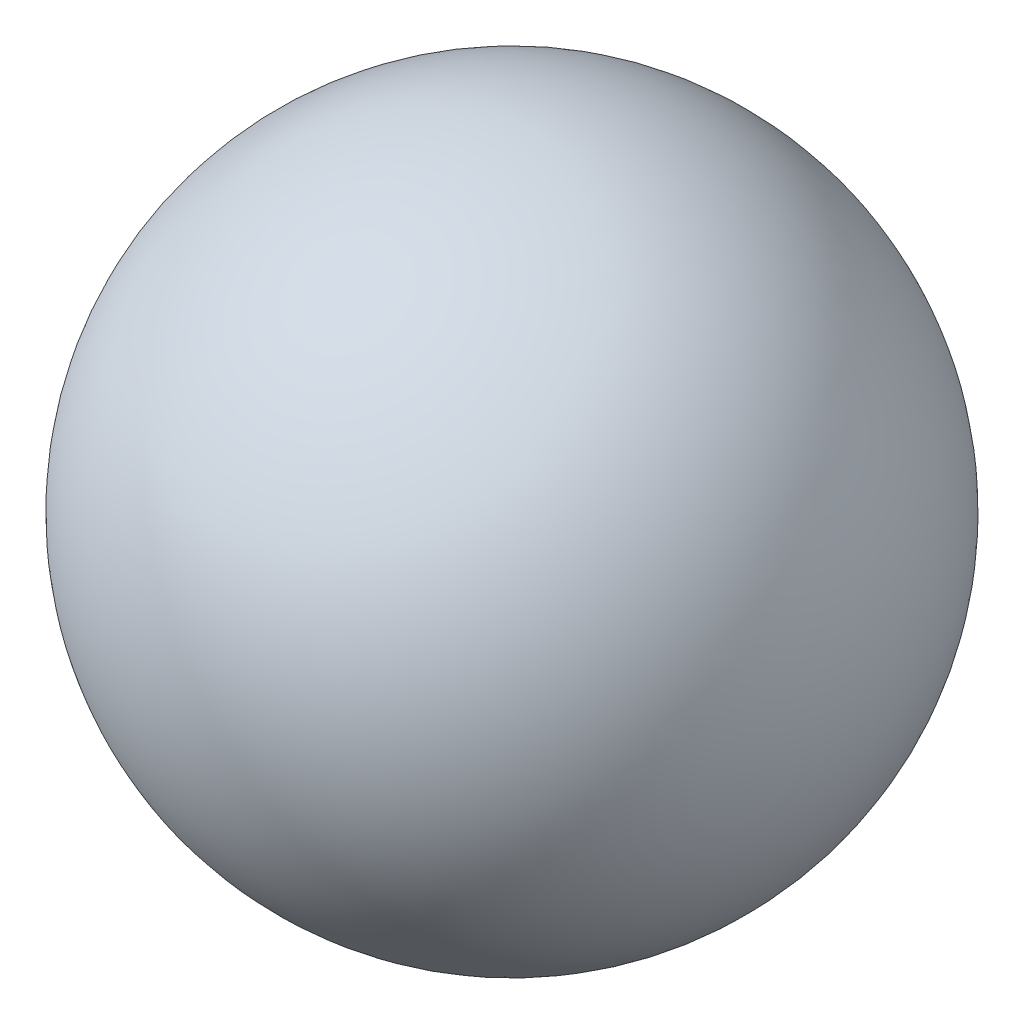
SolidWorks part; units mm, degrees
ref_plane "前基準面" through (0, 0, 0) normal (0, 0, 1) x (1, 0, 0)
ref_plane "上基準面" through (0, 0, 0) normal (0, 1, 0) x (1, 0, 0)
ref_plane "右基準面" through (0, 0, 0) normal (1, 0, 0) x (0, 0, -1)
sketch "草圖1" plane through (0, 0, 0) normal (0, 1, 0) x (1, 0, 0)
  line L0 (0, 16) -> (0, -16)
  line L1 (0, 2.4108) -> (0, -2.4283) construction
  arc A0 (0, -16) -> (0, 16) centre (0, 0) ccw
  dimension "D1" = 32
revolve "旋轉1" add sketch "草圖1" angle 360 about L1
